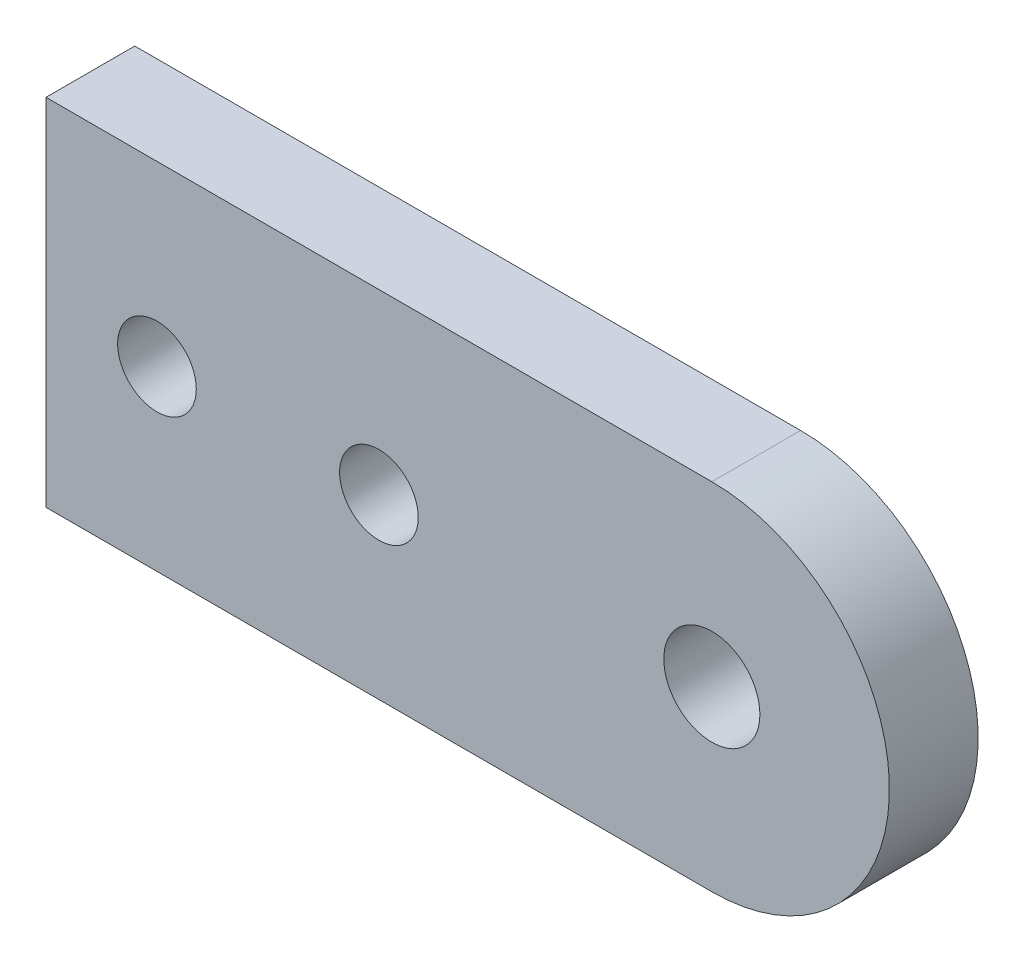
SolidWorks part; units mm, degrees
ref_plane "Front Plane" through (0, 0, 0) normal (0, 0, 1) x (1, 0, 0)
ref_plane "Top Plane" through (0, 0, 0) normal (0, 1, 0) x (1, 0, 0)
ref_plane "Right Plane" through (0, 0, 0) normal (1, 0, 0) x (0, 0, -1)
sketch "Sketch1" plane through (0, 0, 0) normal (0, 0, 1) x (1, 0, 0)
  line L0 (0, 10.16) -> (0, -10.16)
  line L1 (0, -10.16) -> (38.1, -10.16)
  line L2 (38.1, 10.16) -> (0, 10.16)
  arc A0 (38.1, -10.16) -> (38.1, 10.16) centre (38.1, 0) ccw
  point P6 (0, 0)
  dimension "D1" = 20.32
  dimension "D2" = 38.1
extrude "Boss-Extrude1" add sketch "Sketch1" along normal blind 5.08
hole_wizard "M5 Clearance Hole1" positions "Sketch2" profile "Sketch3" hole size "M5" standard "ANSI Metric" end condition through all
sketch "Sketch2" plane through (0, 0, 5.08) normal (0, 0, 1) x (1, 0, 0)
  arc A0 (38.1, -10.16) -> (38.1, 10.16) centre (38.1, 0) ccw construction
  point P0 (38.1, 0)
  point P3 (0, 0)
sketch "Sketch3" plane through (38.1, 0, 5.08) normal (1, 0, 0) x (0, -1, 0)
  line L0 (0, 0) -> (0, 5.08)
  line L1 (0, 5.08) -> (2.75, 5.08)
  line L2 (2.75, 5.08) -> (2.75, 0)
  line L5 (2.75, 0) -> (0, 0)
  line L11 (0, -6.35) -> (0, 107.95) construction
  dimension "Thru Hole Dia." = 5.5
  dimension "Thru Hole Depth" = 5.08
hole_wizard "M4 Clearance Hole1" positions "Sketch4" profile "Sketch5" hole size "M4" standard "ANSI Metric" end condition through all
sketch "Sketch4" plane through (0, 0, 5.08) normal (0, 0, 1) x (1, 0, 0)
  line L6 (0, 10.16) -> (0, -10.16) construction
  point P0 (19.05, -0.0163)
  point P2 (6.35, -0.0045)
  dimension "D1" = 12.7
  dimension "D2" = 6.35
sketch "Sketch5" plane through (19.05, -0.0163, 5.08) normal (1, 0, 0) x (0, -1, 0)
  line L0 (0, 0) -> (0, 5.08)
  line L1 (0, 5.08) -> (2.25, 5.08)
  line L2 (2.25, 5.08) -> (2.25, 0)
  line L5 (2.25, 0) -> (0, 0)
  line L11 (0, -6.35) -> (0, 107.95) construction
  dimension "Thru Hole Dia." = 4.5
  dimension "Thru Hole Depth" = 5.08
